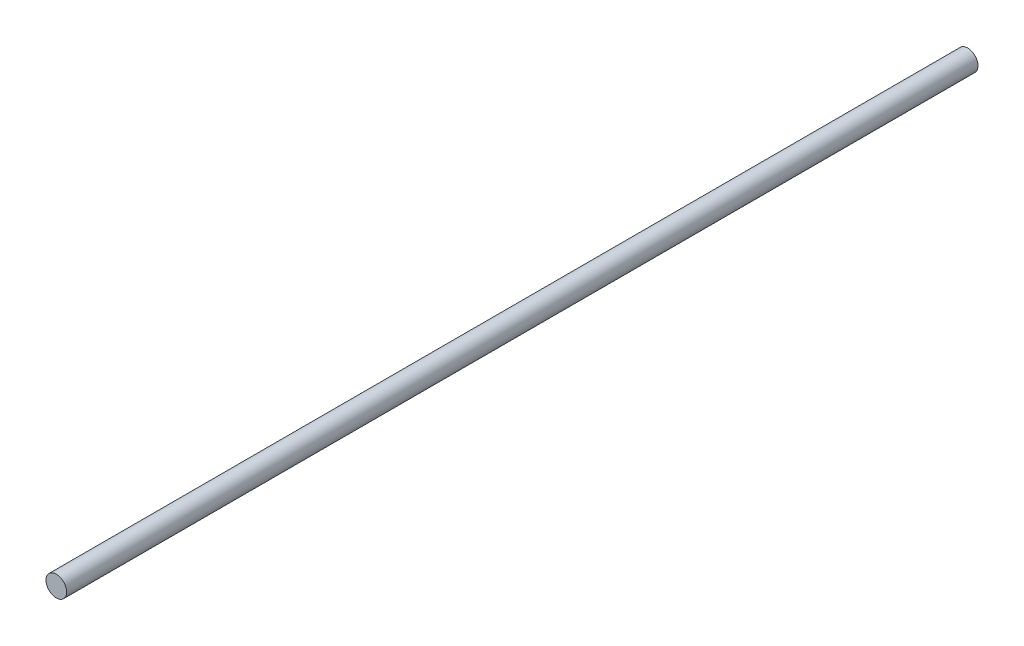
SolidWorks part; units mm, degrees
ref_plane "Front Plane" through (0, 0, 0) normal (0, 0, 1) x (1, 0, 0)
ref_plane "Top Plane" through (0, 0, 0) normal (0, 1, 0) x (1, 0, 0)
ref_plane "Right Plane" through (0, 0, 0) normal (1, 0, 0) x (0, 0, -1)
sketch "Sketch1" plane through (0, 0, 0) normal (0, 0, 1) x (1, 0, 0)
  circle A0 centre (0, 0) radius 3
  dimension "D1" = 6
extrude "Boss-Extrude1" add sketch "Sketch1" along normal blind 265
